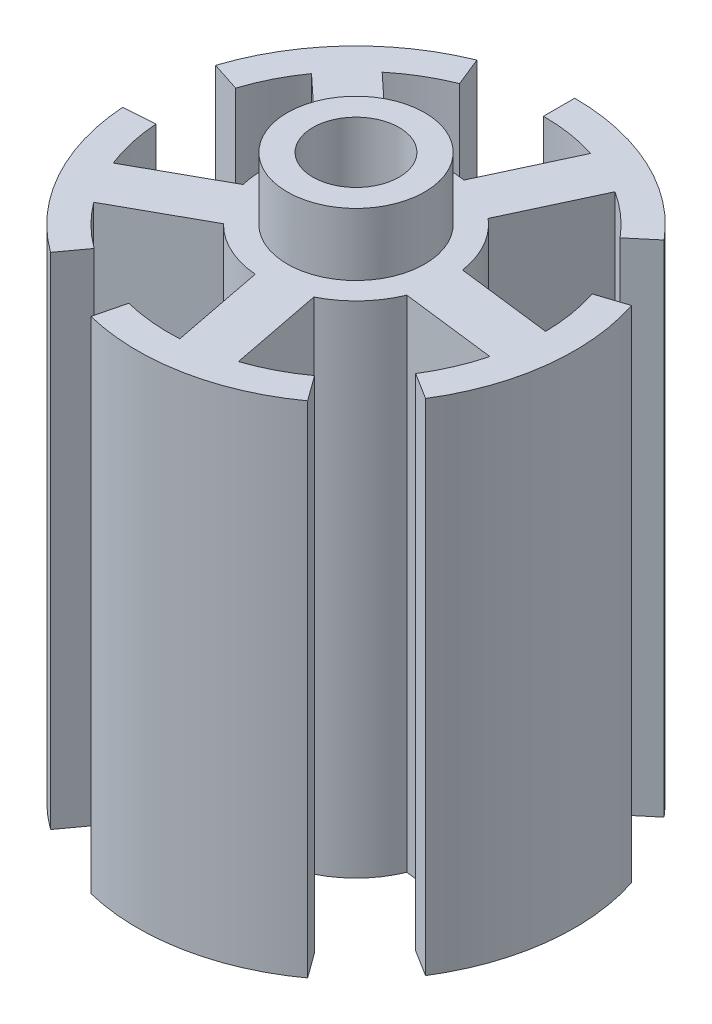
SolidWorks part; units mm, degrees
ref_plane "Front Plane" through (0, 0, 0) normal (0, 0, 1) x (1, 0, 0)
ref_plane "Top Plane" through (0, 0, 0) normal (0, 1, 0) x (1, 0, 0)
ref_plane "Right Plane" through (0, 0, 0) normal (1, 0, 0) x (0, 0, -1)
sketch "Sketch1" plane through (0, 0, 0) normal (0, 1, 0) x (1, 0, 0)
  line L0 (0, 17.5) -> (0, 15)
  line L1 (11.4907, 9.6418) -> (13.4058, 11.2488)
  line L2 (16.6435, 5.4078) -> (14.2658, 4.6353)
  line L3 (12.7207, -7.9488) -> (14.8408, -9.2736)
  line L4 (10.2862, -14.1578) -> (8.8168, -12.1353)
  line L5 (-3.6288, -14.5544) -> (-4.2336, -16.9802)
  line L6 (-10.2862, -14.1578) -> (-8.8168, -12.1353)
  line L7 (-14.9635, -1.0463) -> (-17.4574, -1.2207)
  line L8 (-16.6435, 5.4078) -> (-14.2658, 4.6353)
  line L9 (-5.6191, 13.9078) -> (-6.5556, 16.2257)
  arc A0 (0, 17.5) -> (13.4058, 11.2488) centre (0, 0) cw
  arc A1 (11.4907, 9.6418) -> (0, 15) centre (0, 0) ccw
  arc A2 (16.6435, 5.4078) -> (14.8408, -9.2736) centre (0, 0) cw
  arc A3 (12.7207, -7.9488) -> (14.2658, 4.6353) centre (0, 0) ccw
  arc A4 (10.2862, -14.1578) -> (-4.2336, -16.9802) centre (0, 0) cw
  arc A5 (-3.6288, -14.5544) -> (8.8168, -12.1353) centre (0, 0) ccw
  arc A6 (-10.2862, -14.1578) -> (-17.4574, -1.2207) centre (0, 0) cw
  arc A7 (-14.9635, -1.0463) -> (-8.8168, -12.1353) centre (0, 0) ccw
  arc A8 (-16.6435, 5.4078) -> (-6.5556, 16.2257) centre (0, 0) cw
  arc A9 (-5.6191, 13.9078) -> (-14.2658, 4.6353) centre (0, 0) ccw
  point P25 (0, 0)
  dimension "D1" = 5
extrude "Boss-Extrude2" add sketch "Sketch1" along normal blind 40
sketch "Sketch2" plane through (0, 0, 0) normal (0, 1, 0) x (1, 0, 0)
  line L0 (8.1519, 12.7494) -> (4.5267, 14.4399)
  line L1 (8.1519, 12.7494) -> (1.8723, -0.7172)
  line L2 (4.5267, 14.4399) -> (-1.7529, 0.9732)
  line L3 (1.8723, -0.7172) -> (-1.7529, 0.9732)
  line L4 (14.6445, -3.8131) -> (15.1319, 0.1571)
  line L5 (14.6445, -3.8131) -> (-0.1036, -2.0023)
  line L6 (15.1319, 0.1571) -> (0.3839, 1.9679)
  line L7 (-0.1036, -2.0023) -> (0.3839, 1.9679)
  line L8 (0.8989, -15.106) -> (4.8254, -14.3428)
  line L9 (0.8989, -15.106) -> (-1.9363, -0.5203)
  line L10 (4.8254, -14.3428) -> (1.9902, 0.243)
  line L11 (-1.9363, -0.5203) -> (1.9902, 0.243)
  line L12 (-14.0889, -5.5229) -> (-12.1497, -9.0214)
  line L13 (-14.0889, -5.5229) -> (-1.0931, 1.6808)
  line L14 (-12.1497, -9.0214) -> (0.8461, -1.8177)
  line L15 (-1.0931, 1.6808) -> (0.8461, -1.8177)
  line L16 (-9.6063, 11.6927) -> (-12.3343, 8.7673)
  line L17 (-9.6063, 11.6927) -> (1.2607, 1.559)
  line L18 (-12.3343, 8.7673) -> (-1.4673, -1.3664)
  line L19 (1.2607, 1.559) -> (-1.4673, -1.3664)
  arc A0 (11.4907, 9.6418) -> (0, 15) centre (0, 0) ccw construction
  point P8 (6.3393, 13.5946)
  point P27 (0, 0)
  dimension "D1" = 5
extrude "Boss-Extrude3" add sketch "Sketch2" along normal blind 40 contours L2 L17 L6 L1 L0 | L16 L18 L13 L2 L17 | L18 L13 L12 L14 L9 | L14 L9 L8 L10 L5 | L10 L5 L4 L6 L1 | L7 L15 L14 L5 L10 L1 L3 L11 | L19 L17 L6 L7 | L17 L19 L7 L3 L11 L10 L1 L6 | L19 L7 L6 L17 L2 L13 L15 L3 | L15 L13 L2 L3 | L11 L3 L1 L10 | L11 L19 L18 L9 L14 L5 L7 L15 | L19 L15 L3 L2 L13 L18 L9 L11 | L19 L11 L9 L18 | L15 L7 L5 L14
sketch "Sketch3" plane through (0, 0, 0) normal (0, 1, 0) x (1, 0, 0)
  circle A0 centre (0, 0) radius 7.5
extrude "Boss-Extrude4" add sketch "Sketch3" along normal blind 40
ref_plane "Plane2" through (0, 40, 0) normal (0, 1, 0) x (1, 0, 0)
sketch "Sketch5" plane through (0, 40, 0) normal (0, 1, 0) x (1, 0, 0)
  circle A0 centre (0, 0) radius 5.5
extrude "Boss-Extrude5" add sketch "Sketch5" along normal blind 5
sketch "Sketch4" plane through (0, 0, 0) normal (0, 1, 0) x (1, 0, 0)
  circle A0 centre (0, 0) radius 3.45
extrude "Cut-Extrude1" cut sketch "Sketch4" along normal blind 45
